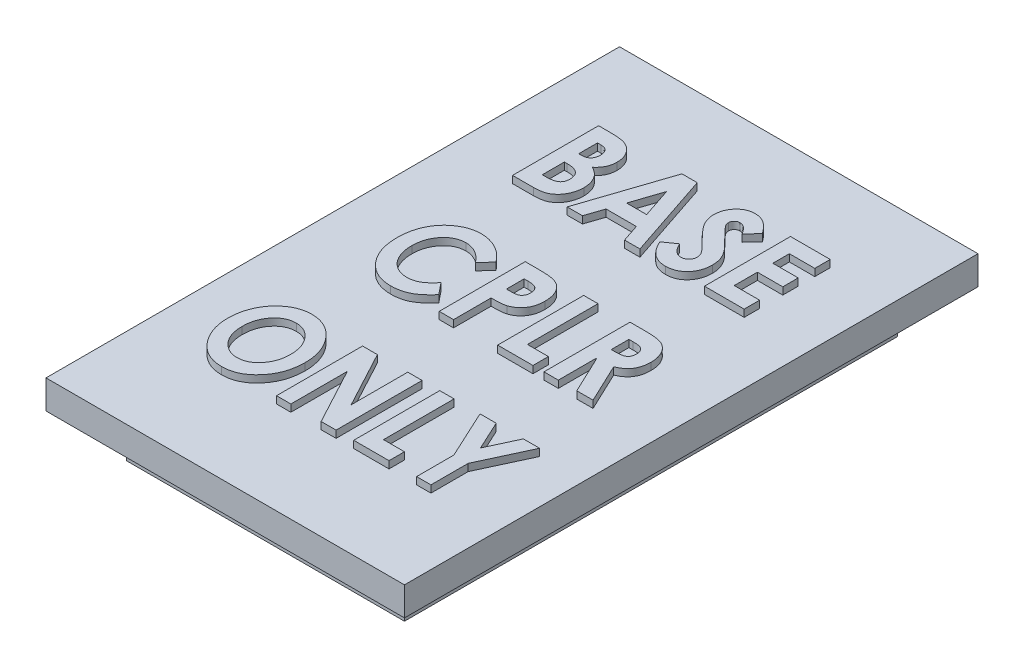
SolidWorks part; units mm, degrees
ref_plane "Front Plane" through (0, 0, 0) normal (0, 0, 1) x (1, 0, 0)
ref_plane "Top Plane" through (0, 0, 0) normal (0, 1, 0) x (1, 0, 0)
ref_plane "Right Plane" through (0, 0, 0) normal (1, 0, 0) x (0, 0, -1)
sketch "Sketch1" plane through (0, 0, 0) normal (0, 1, 0) x (1, 0, 0)
  line L1 (9.7, -17.2) -> (-9.7, -17.2)
  line L2 (9.7, -17.2) -> (9.7, 17.2)
  line L3 (9.7, 17.2) -> (-9.7, 17.2)
  line L4 (-9.7, -17.2) -> (-9.7, 17.2)
  line L5 (9.7, -17.2) -> (-9.7, 17.2) construction
  line L6 (9.7, 17.2) -> (-9.7, -17.2) construction
  point P0 (0, 0)
  dimension "D1" = 19.4
  dimension "D2" = 34.4
extrude "Boss-Extrude1" add sketch "Sketch1" along normal blind 3
sketch "Sketch2" plane through (0, 3, 0) normal (0, 1, 0) x (1, 0, 0)
  line L1 (12.5, -20) -> (-12.5, -20)
  line L2 (12.5, -20) -> (12.5, 20)
  line L3 (12.5, 20) -> (-12.5, 20)
  line L4 (-12.5, -20) -> (-12.5, 20)
  line L5 (12.5, -20) -> (-12.5, 20) construction
  line L6 (12.5, 20) -> (-12.5, -20) construction
  point P0 (0, 0)
  dimension "D1" = 25
  dimension "D2" = 40
extrude "Boss-Extrude2" add sketch "Sketch2" along normal blind 2
sketch "Sketch3" plane through (0, 5, 0) normal (0, 1, 0) x (1, 0, 0)
  line L0 (-12.5, 8) -> (12.5, 8) construction
  line L1 (-12.5, 20) -> (-12.5, -20) construction
  line L2 (12.5, -20) -> (12.5, 20) construction
  line L3 (12.5, 20) -> (-12.5, 20) construction
  text T0 "<b>BASE</b>\r\nCPLR\r\n<b>ONLY</b>" font "Century Gothic" height 6
  dimension "D1" = 12
extrude "Boss-Extrude3" add sketch "Sketch3" along normal blind 0.5
